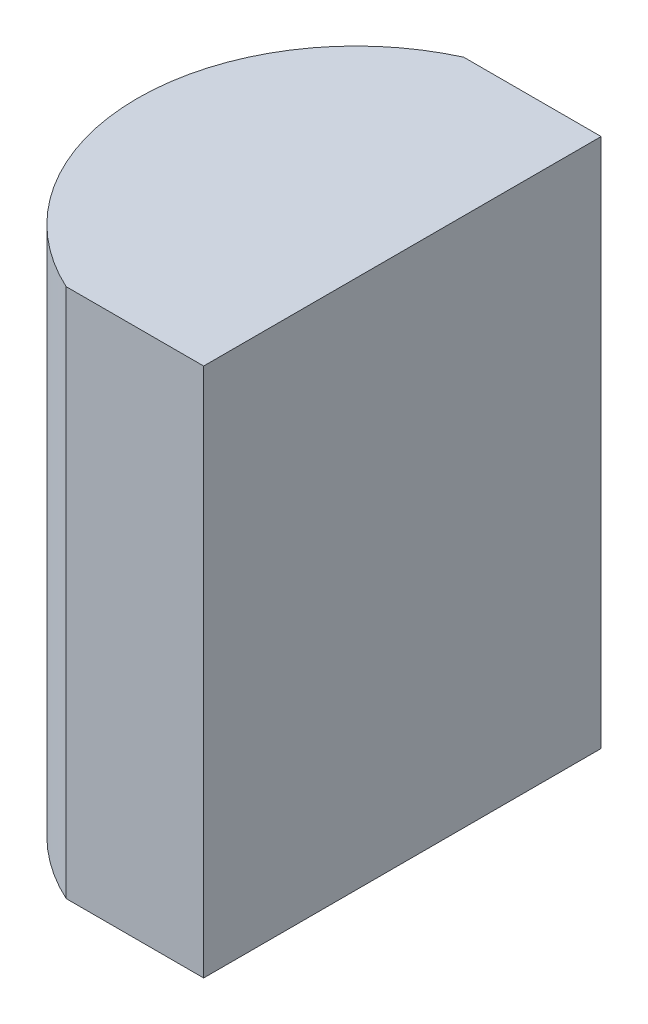
SolidWorks part; units mm, degrees
ref_plane "前视基准面" through (0, 0, 0) normal (0, 0, 1) x (1, 0, 0)
ref_plane "上视基准面" through (0, 0, 0) normal (0, 1, 0) x (1, 0, 0)
ref_plane "右视基准面" through (0, 0, 0) normal (1, 0, 0) x (0, 0, -1)
sketch "草图1" plane through (0, 0, 0) normal (0, 1, 0) x (1, 0, 0)
  line L0 (0, 0) -> (10.0716, 0) construction
  line L1 (2.9804, 3) -> (5.0552, 3)
  line L2 (2.9804, -3) -> (5.0552, -3)
  line L3 (5.0552, 3) -> (5.0552, -3)
  arc A0 (2.9804, 3) -> (2.9804, -3) centre (4.3552, 0) ccw
  point P2 (1.0552, 0)
  point P4 (5.0552, 0)
  point P8 (0, 0)
  dimension "D2" = 3
  dimension "D3" = 3.3
  dimension "D4" = 4
  dimension "D1" = 3
extrude "凸台-拉伸1" add sketch "草图1" along normal blind 8
